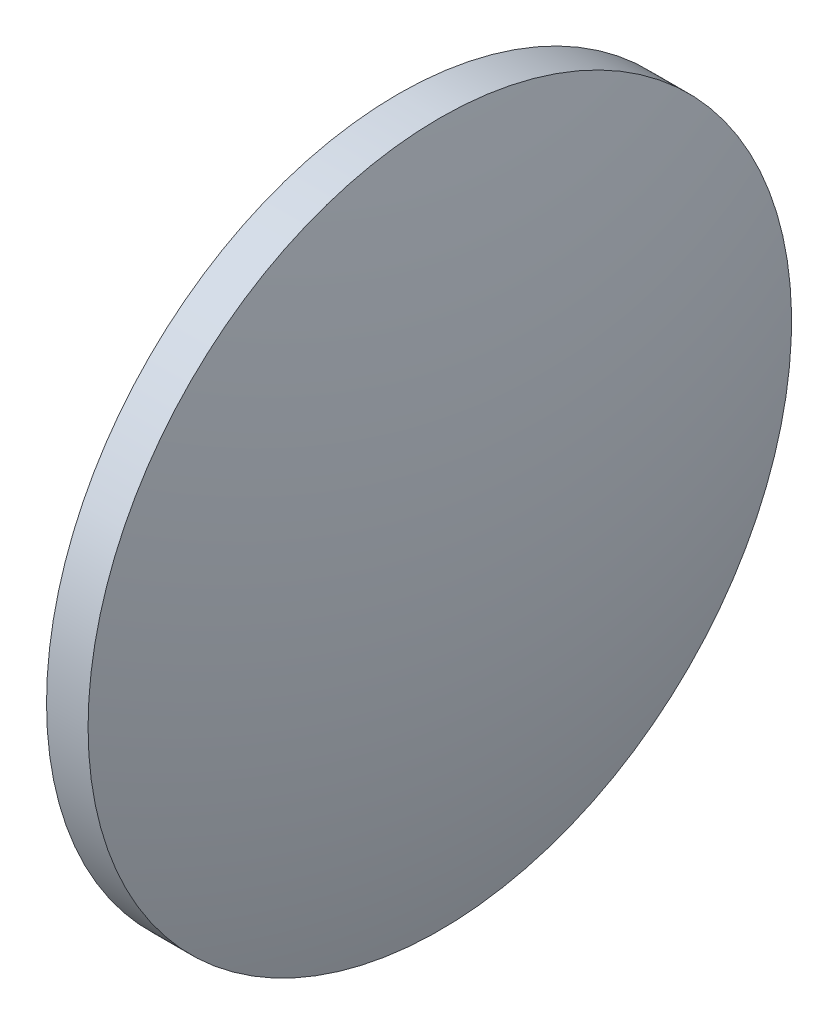
SolidWorks part; units mm, degrees
ref_plane "前视基准面" through (0, 0, 0) normal (0, 0, 1) x (1, 0, 0)
ref_plane "上视基准面" through (0, 0, 0) normal (0, 1, 0) x (1, 0, 0)
ref_plane "右视基准面" through (0, 0, 0) normal (1, 0, 0) x (0, 0, -1)
sketch "草图1" plane through (0, 0, 0) normal (0, 0, 1) x (1, 0, 0)
  line L0 (165.7441, 97.2322) -> (179.7312, 97.2322) construction
  line L1 (171.4164, 122.6322) -> (174.4164, 122.6322)
  line L2 (174.4164, 122.6322) -> (174.4164, 71.8322)
  line L3 (174.4164, 71.8322) -> (171.4164, 71.8322)
  line L4 (171.4164, 71.8322) -> (171.4164, 122.6322)
  arc A0 (171.4164, 122.6322) -> (171.4164, 71.8322) centre (257.9691, 97.2322) ccw
  arc A1 (174.4164, 71.8322) -> (174.4164, 122.6322) centre (87.8637, 97.2322) ccw
  dimension "D1" = 50.8
  dimension "D2" = 3
revolve "旋转1" add sketch "草图1" angle 360 about L0
